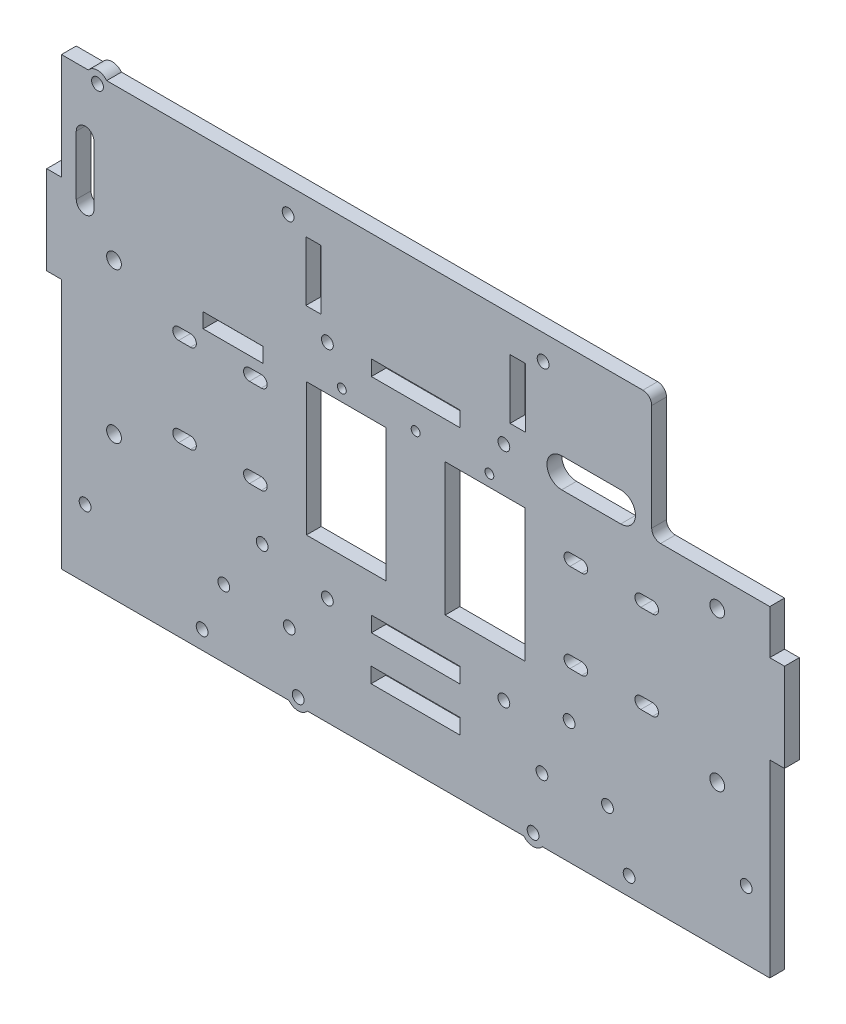
SolidWorks part; units mm, degrees
ref_plane "Front Plane" through (0, 0, 0) normal (0, 0, 1) x (1, 0, 0)
ref_plane "Top Plane" through (0, 0, 0) normal (0, 1, 0) x (1, 0, 0)
ref_plane "Right Plane" through (0, 0, 0) normal (1, 0, 0) x (0, 0, -1)
sketch "Sketch1" plane through (0, 0, 0) normal (0, 0, 1) x (1, 0, 0)
  line L1 (-120, 75.5) -> (120, 75.5)
  line L2 (-120, 75.5) -> (-120, -75.5)
  line L3 (-120, -75.5) -> (120, -75.5)
  line L4 (120, 75.5) -> (120, -75.5)
  dimension "D1" = 240
  dimension "D2" = 151
  dimension "D3" = 75.5
  dimension "D4" = 120
extrude "Boss-Extrude1" add sketch "Sketch1" along normal blind 5
sketch "Sketch2" plane through (0, 0, 0) normal (0, 0, -1) x (-1, 0, 0)
  line L4 (10, 21) -> (37, 21)
  line L5 (37, 21) -> (37, -24)
  line L6 (37, -24) -> (10, -24)
  line L7 (10, -24) -> (10, 21)
  line L8 (0, 0) -> (-98.0945, 0) construction
  line L9 (-120, 75.5) -> (120, 75.5) construction
  line L10 (120, -75.5) -> (-120, -75.5) construction
  line L11 (0, 75.5) -> (0, -75.5) construction
  line L14 (-10, -24) -> (-10, 21)
  line L15 (-37, -24) -> (-10, -24)
  line L16 (-37, 21) -> (-37, -24)
  line L17 (-10, 21) -> (-37, 21)
  dimension "D1" = 45
  dimension "D2" = 27
  dimension "D3" = 21
  dimension "D4" = 10
extrude "Cut-Extrude1" cut sketch "Sketch2" against normal blind 10
sketch "Sketch11" plane through (0, 0, 0) normal (0, 0, -1) x (-1, 0, 0)
  line L0 (0, 0) -> (-153.5827, 0) construction
  line L1 (0, 0) -> (0, 92.8663) construction
  line L2 (-120, 75.5) -> (120, 75.5) construction
  line L3 (20, 16) -> (-27, 16)
  line L4 (20, 16) -> (20, 75.5)
  line L5 (20, 75.5) -> (-27, 75.5)
  line L6 (-27, 16) -> (-27, 75.5)
  dimension "D1" = 16
  dimension "D2" = 20
  dimension "D3" = 47
extrude "Cut-Extrude8" [suppressed] cut sketch "Sketch11" against normal blind 10
sketch "Sketch12" plane through (0, 0, 0) normal (0, 0, -1) x (-1, 0, 0)
  line L0 (0, 0) -> (0, 113.3526) construction
  line L1 (0, 0) -> (164.3438, 0) construction
  circle A0 centre (23, 65) radius 2
  circle A1 centre (23, 45) radius 2
  dimension "D1" = 4
  dimension "D2" = 4
  dimension "D3" = 23
  dimension "D6" = 20
  dimension "D7" = 65
extrude "Cut-Extrude9" [suppressed] cut sketch "Sketch12" against normal blind 5
sketch "Sketch13" [suppressed] plane through (0, 0, 0) normal (0, 0, -1) x (-1, 0, 0)
  line L0 (0, 0) -> (61.643, 0) construction
  line L1 (0, 0) -> (0, 63.8684) construction
  circle A0 centre (23, 65) radius 4
  circle A1 centre (23, 45) radius 4
  circle A2 centre (23, 65) radius 2
  circle A3 centre (23, 45) radius 2
  dimension "D1" = 8
  dimension "D2" = 8
  dimension "D3" = 4
  dimension "D4" = 4
extrude "Boss-Extrude5" [suppressed] add sketch "Sketch13" against normal blind 5
ref_plane "Plane1" [suppressed] through (3.5, 0, 0) normal (1, 0, 0) x (0, 0, -1)
mirror "Mirror1" [suppressed] about plane through (3.5, 0, 0) normal (1, 0, 0)
sketch "Sketch14" plane through (0, 0, 0) normal (0, 0, -1) x (-1, 0, 0)
  line L0 (-37, -1.5) -> (-94.1401, -1.5) construction
  line L1 (-37, 21) -> (-37, -24) construction
  line L2 (-37, -1.5) -> (-37, 9.4006) construction
  line L3 (-56.3, 13.46) -> (-52.3, 13.46) construction
  line L4 (-56.3, 15.46) -> (-52.3, 15.46)
  line L5 (-56.3, 11.46) -> (-52.3, 11.46)
  line L6 (-80.3, 13.46) -> (-76.3, 13.46) construction
  line L7 (-80.3, 15.46) -> (-76.3, 15.46)
  line L8 (-80.3, 11.46) -> (-76.3, 11.46)
  line L9 (-80.3, -16.54) -> (-76.3, -16.54) construction
  line L10 (-80.3, -14.54) -> (-76.3, -14.54)
  line L11 (-80.3, -18.54) -> (-76.3, -18.54)
  line L12 (-56.3, -16.54) -> (-52.3, -16.54) construction
  line L13 (-56.3, -14.54) -> (-52.3, -14.54)
  line L14 (-56.3, -18.54) -> (-52.3, -18.54)
  line L15 (0, 0) -> (0, -41.609) construction
  line L16 (37, -1.5) -> (94.1401, -1.5) construction
  line L17 (56.3, -16.54) -> (52.3, -16.54) construction
  line L18 (56.3, -14.54) -> (52.3, -14.54)
  line L19 (56.3, -18.54) -> (52.3, -18.54)
  line L20 (80.3, -16.54) -> (76.3, -16.54) construction
  line L21 (80.3, -14.54) -> (76.3, -14.54)
  line L22 (80.3, -18.54) -> (76.3, -18.54)
  line L23 (80.3, 13.46) -> (76.3, 13.46) construction
  line L24 (80.3, 15.46) -> (76.3, 15.46)
  line L25 (80.3, 11.46) -> (76.3, 11.46)
  line L26 (56.3, 13.46) -> (52.3, 13.46) construction
  line L27 (56.3, 15.46) -> (52.3, 15.46)
  line L28 (56.3, 11.46) -> (52.3, 11.46)
  arc A0 (56.3, -14.54) -> (56.3, -18.54) centre (56.3, -16.54) cw
  arc A2 (52.3, -18.54) -> (52.3, -14.54) centre (52.3, -16.54) cw
  arc A4 (80.3, -14.54) -> (80.3, -18.54) centre (80.3, -16.54) cw
  arc A6 (76.3, -18.54) -> (76.3, -14.54) centre (76.3, -16.54) cw
  arc A8 (-56.3, 15.46) -> (-56.3, 11.46) centre (-56.3, 13.46) ccw
  arc A9 (-52.3, 11.46) -> (-52.3, 15.46) centre (-52.3, 13.46) ccw
  arc A10 (-80.3, 15.46) -> (-80.3, 11.46) centre (-80.3, 13.46) ccw
  arc A11 (-76.3, 11.46) -> (-76.3, 15.46) centre (-76.3, 13.46) ccw
  arc A12 (-80.3, -14.54) -> (-80.3, -18.54) centre (-80.3, -16.54) ccw
  arc A13 (-76.3, -18.54) -> (-76.3, -14.54) centre (-76.3, -16.54) ccw
  arc A14 (-56.3, -14.54) -> (-56.3, -18.54) centre (-56.3, -16.54) ccw
  arc A15 (-52.3, -18.54) -> (-52.3, -14.54) centre (-52.3, -16.54) ccw
  arc A16 (80.3, 15.46) -> (80.3, 11.46) centre (80.3, 13.46) cw
  arc A17 (76.3, 11.46) -> (76.3, 15.46) centre (76.3, 13.46) cw
  arc A18 (56.3, 15.46) -> (56.3, 11.46) centre (56.3, 13.46) cw
  arc A19 (52.3, 11.46) -> (52.3, 15.46) centre (52.3, 13.46) cw
  point P9 (54.3, -16.54)
  point P15 (-54.3, 13.46)
  point P22 (-78.3, 13.46)
  point P27 (-78.3, -16.54)
  point P34 (-54.3, -16.54)
  point P47 (78.3, -16.54)
  point P54 (78.3, 13.46)
  point P61 (54.3, 13.46)
  dimension "D2" = 14.96
  dimension "D3" = 15.04
  dimension "D4" = 41.3
  dimension "D5" = 4
  dimension "D6" = 4
  dimension "D7" = 4
  dimension "D8" = 4
  dimension "D9" = 41.3
  dimension "D10" = 17.3
  dimension "D11" = 4
  dimension "D12" = 4
  dimension "D13" = 4
  dimension "D14" = 4
  dimension "D15" = 17.3
extrude "Cut-Extrude10" cut sketch "Sketch14" against normal blind 5
sketch "Sketch15" plane through (0, 0, 0) normal (0, 0, -1) x (-1, 0, 0)
  line L0 (-37, -1.5) -> (-108.3455, -1.5) construction
  line L1 (-37, 21) -> (-37, -24) construction
  line L2 (0, 0) -> (0, 43.9144) construction
  line L3 (37, -1.5) -> (108.3455, -1.5) construction
  circle A1 centre (-102.2, -27) radius 2.5
  circle A3 centre (-102.2, 24) radius 2.5
  circle A4 centre (102.2, 24) radius 2.5
  circle A5 centre (102.2, -27) radius 2.5
  dimension "D1" = 5
  dimension "D2" = 5
  dimension "D3" = 25.5
  dimension "D4" = 25.5
  dimension "D5" = 102.2
extrude "Cut-Extrude11" cut sketch "Sketch15" against normal blind 10
sketch "Sketch16" plane through (0, 0, 0) normal (0, 0, -1) x (-1, 0, 0)
  line L0 (0, 0) -> (113.7141, 0) construction
  line L1 (0, 0) -> (0, 64.2652) construction
  circle A1 centre (59.5, 57.4178) radius 2
  circle A3 centre (59.5, 37.4178) radius 2
  circle A5 centre (59.5, 17.4178) radius 2
  dimension "D1" = 4
  dimension "D2" = 4
  dimension "D3" = 4
  dimension "D4" = 59.5
  dimension "D5" = 17.4178
  dimension "D6" = 20
  dimension "D7" = 20
extrude "Cut-Extrude12" [suppressed] cut sketch "Sketch16" against normal blind 10
sketch "Sketch17" plane through (0, 0, 0) normal (0, 0, -1) x (-1, 0, 0)
  line L0 (0, 0) -> (61.7311, 0) construction
  line L1 (0, 0) -> (0, 40.2669) construction
  line L2 (15, 33.5) -> (15, 38.7)
  line L7 (-15, 38.7) -> (15, 38.7)
  line L8 (-15, 33.5) -> (-15, 38.7)
  line L9 (-15, 33.5) -> (15, 33.5)
  line L12 (-15, -36.5) -> (15, -36.5)
  line L13 (-15, -36.5) -> (-15, -41.7)
  line L14 (-15, -41.7) -> (15, -41.7)
  line L15 (15, -36.5) -> (15, -41.7)
  circle A0 centre (-29.9, -39.1) radius 2
  circle A1 centre (29.9, -39.1) radius 2
  circle A2 centre (-29.9, 36.1) radius 2
  circle A3 centre (29.9, 36.1) radius 2
  point P25 (-15, 36.1)
  point P27 (-15, -39.1)
  dimension "D10" = 4
  dimension "D11" = 4
  dimension "D12" = 4
  dimension "D13" = 4
  dimension "D1" = 33.5
  dimension "D2" = 15
  dimension "D3" = 90
  dimension "D4" = 30
  dimension "D5" = 5.2
  dimension "D6" = 36.5
  dimension "D7" = 5.2
  dimension "D8" = 15
  dimension "D9" = 30
  dimension "D14" = 14.9
  dimension "D15" = 14.9
  dimension "D16" = 14.9
  dimension "D17" = 14.9
extrude "Cut-Extrude13" cut sketch "Sketch17" against normal blind 10
sketch "Sketch20" plane through (0, 0, 0) normal (0, 0, -1) x (-1, 0, 0)
  line L12 (0, 0) -> (0, 66.2601) construction
  line L13 (0, 0) -> (-22.6234, 0) construction
  circle A0 centre (43.2, 67) radius 2
  circle A1 centre (-43.2, 67) radius 2
  point P15 (-11.3117, 0)
  dimension "D1" = 4
  dimension "D2" = 4
  dimension "D3" = 43.2
  dimension "D4" = 67
  dimension "D5" = 43.2
  dimension "D6" = 67
extrude "Cut-Extrude15" cut sketch "Sketch20" against normal blind 5
sketch "Sketch23" plane through (0, 0, 0) normal (0, 0, -1) x (-1, 0, 0)
  line L8 (0, 0) -> (0, -64.892) construction
  line L9 (0, 0) -> (29.1708, 0) construction
  circle A0 centre (42.8, -54) radius 2
  circle A1 centre (-42.8, -54) radius 2
  dimension "D1" = 4
  dimension "D2" = 54
  dimension "D3" = 42.8
extrude "Cut-Extrude16" cut sketch "Sketch23" against normal blind 5
sketch "Sketch24" plane through (0, 0, 0) normal (0, 0, -1) x (-1, 0, 0)
  line L1 (-15.1, -56.7) -> (15.1, -56.7)
  line L3 (-15.1, -51.5) -> (-15.1, -56.7)
  line L6 (15.1, -51.5) -> (15.1, -56.7)
  line L7 (-15.1, -51.5) -> (15.1, -51.5)
  line L8 (0, 0) -> (0, -47.2629) construction
  line L9 (0, 0) -> (-25.5979, 0) construction
  dimension "D1" = 51.5
  dimension "D2" = 5.2
  dimension "D3" = 15.1
  dimension "D4" = 15.1
extrude "Cut-Extrude17" cut sketch "Sketch24" against normal blind 5
sketch "Sketch27" plane through (0, 0, 0) normal (0, 0, -1) x (-1, 0, 0)
  line L0 (0, 0) -> (0, 10.7303) construction
  line L1 (0, 0) -> (-15.1095, 0) construction
  circle A1 centre (-25, 25) radius 1.5
  circle A3 centre (0, 25) radius 1.5
  circle A5 centre (25, 25) radius 1.5
  dimension "D1" = 3
  dimension "D2" = 3
  dimension "D3" = 3
  dimension "D4" = 25
  dimension "D5" = 25
  dimension "D6" = 25
extrude "Cut-Extrude20" cut sketch "Sketch27" against normal blind 10
sketch "Sketch28" plane through (0, 0, 5) normal (0, 0, 1) x (1, 0, 0)
  line L0 (0, 0) -> (0, -94.1859) construction
  line L1 (0, 0) -> (142.2431, 0) construction
  circle A1 centre (112, -52.5) radius 2
  circle A3 centre (65, -52.5) radius 2
  circle A4 centre (-65, -52.5) radius 2
  circle A5 centre (-112, -52.5) radius 2
  dimension "D2" = 4
  dimension "D3" = 4
  dimension "D1" = 47
  dimension "D4" = 65
  dimension "D5" = 52.5
extrude "Cut-Extrude21" cut sketch "Sketch28" against normal blind 10
sketch "Sketch29" plane through (0, 0, 0) normal (0, 0, -1) x (-1, 0, 0)
  line L1 (0, 0) -> (0, 54.3151) construction
  line L3 (0, 0) -> (50.4832, 0) construction
  circle A0 centre (62, 21.5) radius 2
  dimension "D1" = 4
  dimension "D2" = 21.5
  dimension "D3" = 62
extrude "Cut-Extrude22" [suppressed] cut sketch "Sketch29" against normal blind 10
sketch "Sketch30" plane through (0, 0, 0) normal (0, 0, -1) x (-1, 0, 0)
  line L1 (0, 0) -> (31.6548, 0) construction
  line L3 (0, 0) -> (0, -25.192) construction
  circle A0 centre (-24.8, -29.5) radius 2
  circle A1 centre (24.8, -29.5) radius 2
  dimension "D1" = 4
  dimension "D2" = 4
  dimension "D3" = 24.8
  dimension "D4" = 24.8
  dimension "D5" = 29.5
extrude "Cut-Extrude23" [suppressed] cut sketch "Sketch30" against normal blind 10
sketch "Sketch31" plane through (0, 0, 0) normal (0, 0, -1) x (-1, 0, 0)
  line L0 (0, 0) -> (0, -47.0899) construction
  line L1 (0, 0) -> (74.357, 0) construction
  circle A2 centre (72.3457, -69.3397) radius 2
  circle A5 centre (-72.3457, -69.3397) radius 2
  dimension "D1" = 72.3457
  dimension "D2" = 4
  dimension "D3" = 69.3397
extrude "Cut-Extrude24" cut sketch "Sketch31" against normal blind 10
sketch "Sketch32" plane through (0, 0, 0) normal (0, 0, -1) x (-1, 0, 0)
  line L0 (0, 0) -> (0, -27.0563) construction
  line L1 (0, 0) -> (46.0859, 0) construction
  circle A1 centre (52.0058, -34.11) radius 2
  circle A2 centre (-52.0058, -34.11) radius 2
  dimension "D1" = 4
  dimension "D2" = 34.11
  dimension "D3" = 52.0058
extrude "Cut-Extrude25" cut sketch "Sketch32" against normal blind 10
sketch "Sketch34" plane through (0, 0, 0) normal (0, 0, -1) x (-1, 0, 0)
  line L0 (-120, -75.5) -> (-120, 75.5) construction
  line L1 (-120, 75.5) -> (-80, 75.5)
  line L2 (-120, 75.5) -> (-120, 33.5)
  line L3 (-120, 33.5) -> (-80, 33.5)
  line L4 (-80, 75.5) -> (-80, 33.5)
  line L7 (-120, 75.5) -> (120, 75.5) construction
  dimension "D1" = 42
  dimension "D3" = 40
extrude "Cut-Extrude26" cut sketch "Sketch34" against normal blind 10
sketch "Sketch35" plane through (0, 0, 0) normal (0, 0, -1) x (-1, 0, 0)
  line L0 (-49.5, 37.5) -> (-69.5, 37.5) construction
  line L1 (-49.5, 32.5) -> (-69.5, 32.5)
  line L2 (-49.5, 42.5) -> (-69.5, 42.5)
  line L3 (-120, -75.5) -> (-120, 33.5) construction
  line L4 (-80, 75.5) -> (120, 75.5) construction
  arc A0 (-49.5, 32.5) -> (-49.5, 42.5) centre (-49.5, 37.5) ccw
  arc A1 (-69.5, 42.5) -> (-69.5, 32.5) centre (-69.5, 37.5) ccw
  point P2 (-59.5, 37.5)
  dimension "D1" = 10
  dimension "D2" = 60.5
  dimension "D3" = 33
  dimension "D4" = 20
extrude "Cut-Extrude27" cut sketch "Sketch35" against normal blind 10
sketch "Sketch36" plane through (0, 0, 0) normal (0, 0, -1) x (-1, 0, 0)
  line L0 (112, 35.5) -> (112, 55.5) construction
  line L1 (109, 35.5) -> (109, 55.5)
  line L2 (115, 35.5) -> (115, 55.5)
  line L3 (120, 75.5) -> (120, -75.5) construction
  line L4 (-80, 75.5) -> (120, 75.5) construction
  arc A0 (109, 35.5) -> (115, 35.5) centre (112, 35.5) ccw
  arc A1 (115, 55.5) -> (109, 55.5) centre (112, 55.5) ccw
  point P2 (112, 45.5)
  dimension "D1" = 20
  dimension "D2" = 5
  dimension "D3" = 6
  dimension "D4" = 20
extrude "Cut-Extrude28" cut sketch "Sketch36" against normal blind 10
sketch "Sketch37" plane through (0, 0, 5) normal (0, 0, 1) x (1, 0, 0)
  line L1 (37.2, 43.25) -> (37.2, 63.45)
  line L3 (37.2, 63.45) -> (32, 63.45)
  line L5 (32, 43.25) -> (32, 63.45)
  line L7 (37.2, 43.25) -> (32, 43.25)
  line L8 (0, 0) -> (0, 66.0689) construction
  line L9 (-37.2, 43.25) -> (-32, 43.25)
  line L10 (-32, 43.25) -> (-32, 63.45)
  line L11 (-37.2, 63.45) -> (-32, 63.45)
  line L12 (-37.2, 43.25) -> (-37.2, 63.45)
  line L13 (0, 0) -> (45.9308, 0) construction
  dimension "D1" = 5.2
  dimension "D2" = 20.2
  dimension "D3" = 43.25
extrude "Cut-Extrude29" cut sketch "Sketch37" against normal blind 10
sketch "Sketch38" plane through (0, 0, 5) normal (0, 0, 1) x (1, 0, 0)
  line L4 (-51.8, 24.02) -> (-51.8, 19)
  line L5 (-72, 19) -> (-51.8, 19)
  line L6 (-72, 24.02) -> (-72, 19)
  line L7 (-72, 24.02) -> (-51.8, 24.02)
  dimension "D1" = 5.02
  dimension "D2" = 20.2
extrude "Cut-Extrude30" cut sketch "Sketch38" against normal blind 5
sketch "Sketch39" plane through (0, 0, 0) normal (0, 0, -1) x (-1, 0, 0)
  circle A0 centre (107.8, 73) radius 2
  dimension "D1" = 4
extrude "Cut-Extrude31" cut sketch "Sketch39" against normal blind 5
sketch "Sketch40" plane through (0, 0, 0) normal (0, 0, -1) x (-1, 0, 0)
  circle A0 centre (107.8, 73) radius 2
  circle A1 centre (107.8, 73) radius 4
  dimension "D1" = 8
extrude "Boss-Extrude6" add sketch "Sketch40" against normal blind 5
fillet "Fillet1" radius 3 1 edges at (80, 33.5, 2.5)
sketch "Sketch41" plane through (0, 0, 0) normal (0, 0, -1) x (-1, 0, 0)
  circle A0 centre (39.8, -73) radius 2
  circle A1 centre (-39.8, -73) radius 2
  dimension "D1" = 4
  dimension "D2" = 4
extrude "Cut-Extrude32" cut sketch "Sketch41" against normal blind 5
sketch "Sketch42" plane through (0, 0, 0) normal (0, 0, -1) x (-1, 0, 0)
  circle A0 centre (-39.8, -73) radius 2
  circle A1 centre (-39.8, -73) radius 4
  circle A2 centre (39.8, -73) radius 2
  circle A3 centre (39.8, -73) radius 4
  dimension "D1" = 4
  dimension "D2" = 8
  dimension "D3" = 4
  dimension "D4" = 8
extrude "Boss-Extrude7" add sketch "Sketch42" against normal blind 5
sketch "Sketch43" plane through (0, 0, 0) normal (0, 0, -1) x (-1, 0, 0)
  line L0 (-120, -75.5) -> (-120, 33.5) construction
  line L1 (-120, 18.5) -> (-125, 18.5)
  line L2 (-120, 18.5) -> (-120, -11.5)
  line L3 (-120, -11.5) -> (-125, -11.5)
  line L4 (-125, 18.5) -> (-125, -11.5)
  line L5 (120, 75.5) -> (120, -75.5) construction
  line L10 (-42.9225, -75.5) -> (-120, -75.5) construction
  line L11 (120, 39.5) -> (125, 39.5)
  line L12 (120, 39.5) -> (120, 9.5)
  line L13 (120, 9.5) -> (125, 9.5)
  line L14 (125, 39.5) -> (125, 9.5)
  line L15 (120, -75.5) -> (42.9225, -75.5) construction
  point P16 (-120, 3.5)
  dimension "D1" = 5
  dimension "D2" = 64
  dimension "D3" = 30
  dimension "D4" = 85
  dimension "D5" = 30
  dimension "D6" = 5
extrude "Boss-Extrude8" add sketch "Sketch43" against normal blind 5
fillet "Fillet2" radius 3 1 edges at (80, 75.5, 2.5)
